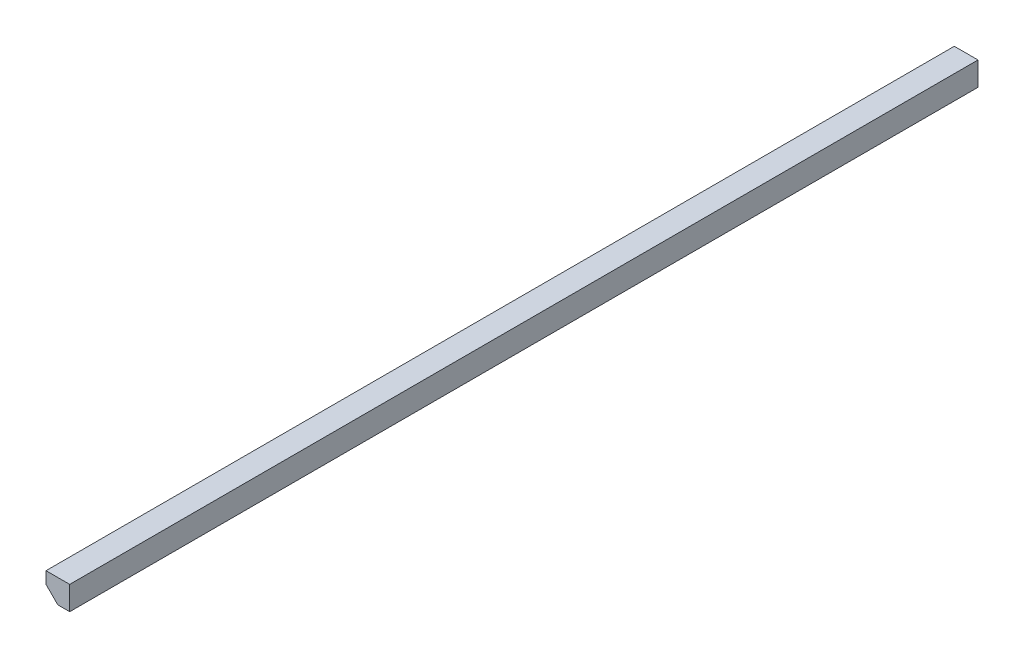
SolidWorks part; units mm, degrees
material "Cedar"
ref_plane "Front" through (0, 0, 0) normal (0, 0, 1) x (1, 0, 0)
ref_plane "Top" through (0, 0, 0) normal (0, 1, 0) x (1, 0, 0)
ref_plane "Right" through (0, 0, 0) normal (1, 0, 0) x (0, 0, -1)
sketch "Sketch1" plane through (0, 0, 0) normal (0, 0, 1) x (1, 0, 0)
  line L0 (0, 0) -> (19.05, 0) construction
  line L1 (19.05, 0) -> (19.05, 19.05)
  line L2 (19.05, 19.05) -> (0, 19.05)
  line L3 (0, 19.05) -> (0, 0) construction
  line L4 (0, 9.525) -> (9.525, 0)
  line L5 (9.525, 0) -> (19.05, 0)
  line L6 (0, 19.05) -> (0, 9.525)
extrude "Extrude1" add sketch "Sketch1" along normal mid plane 730.25
